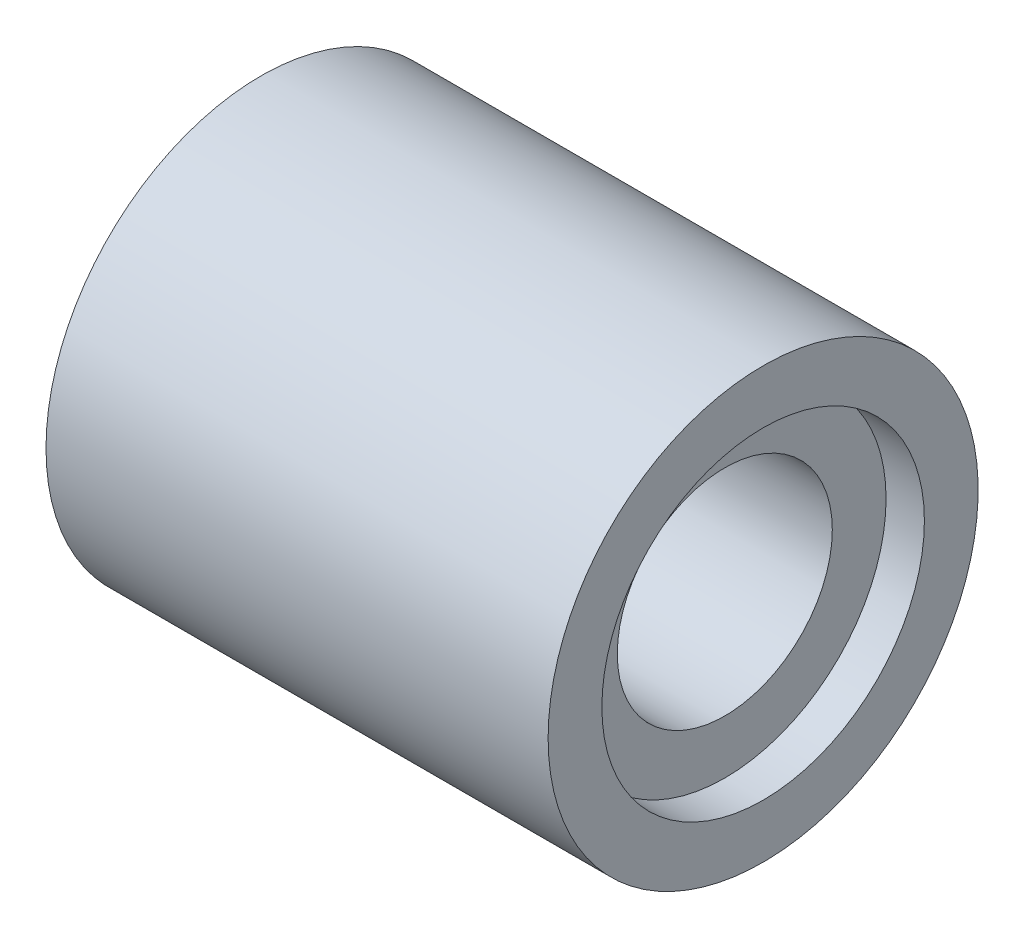
SolidWorks part; units mm, degrees
ref_plane "Front Plane" through (0, 0, 0) normal (0, 0, 1) x (1, 0, 0)
ref_plane "Top Plane" through (0, 0, 0) normal (0, 1, 0) x (1, 0, 0)
ref_plane "Right Plane" through (0, 0, 0) normal (1, 0, 0) x (0, 0, -1)
sketch "Sketch1" plane through (0, 0, 0) normal (0, 0, 1) x (1, 0, 0)
  line L0 (-29.384, 0) -> (35.5601, 0) construction
  line L1 (-25.3535, 20) -> (-25.3535, 15)
  line L2 (-25.3535, 15) -> (-21.3682, 15)
  line L3 (-21.3682, 15) -> (-21.3682, 10)
  line L4 (-21.3682, 10) -> (17.7856, 10)
  line L5 (17.7856, 10) -> (17.7856, 15)
  line L7 (21.3514, 15) -> (21.3514, 20)
  line L8 (21.3514, 20) -> (-25.3535, 20)
  line L9 (17.7856, 15) -> (21.3514, 15)
  dimension "D1" = 20
  dimension "D2" = 15
  dimension "D3" = 40
revolve "Revolve1" add sketch "Sketch1" angle 360 about L0
